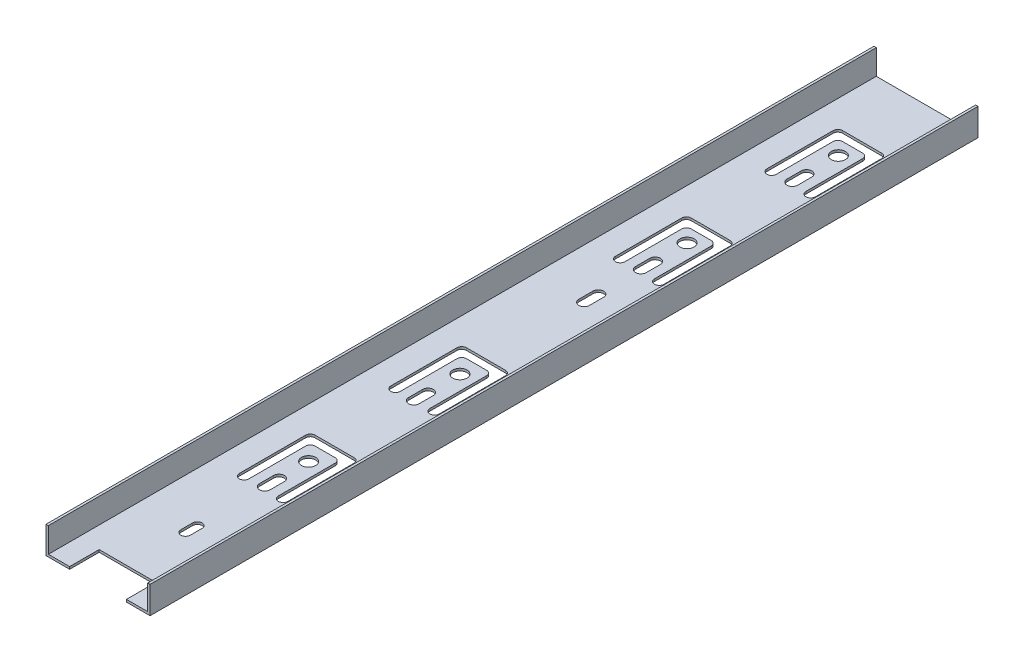
SolidWorks part; units mm, degrees
ref_plane "前视基准面" through (0, 0, 0) normal (0, 0, 1) x (1, 0, 0)
ref_plane "上视基准面" through (0, 0, 0) normal (0, 1, 0) x (1, 0, 0)
ref_plane "右视基准面" through (0, 0, 0) normal (1, 0, 0) x (0, 0, -1)
sketch "草图1" plane through (0, 0, 0) normal (0, 0, 1) x (1, 0, 0)
  line L0 (-12.1861, 22.9643) -> (-12.1861, -29.0019) construction
  line L1 (-34.1861, 5.4117) -> (-33.1861, 5.4117)
  line L2 (-34.1861, 5.4117) -> (-34.1861, -6.0883)
  line L3 (-34.1861, -6.0883) -> (9.8139, -6.0883)
  line L4 (9.8139, 5.4117) -> (9.8139, -6.0883)
  line L6 (-33.1861, 5.4117) -> (-33.1861, -5.0883)
  line L7 (-33.1861, -5.0883) -> (8.8139, -5.0883)
  line L8 (8.8139, 5.4117) -> (8.8139, -5.0883)
  line L9 (8.8139, 5.4117) -> (9.8139, 5.4117)
  dimension "D1" = 11.5
  dimension "D2" = 44
  dimension "D3" = 1
  dimension "D4" = 1
extrude "凸台-拉伸1" add sketch "草图1" along normal blind 350
sketch "草图2" plane through (0, -6.0883, 0) normal (0, -1, 0) x (1, 0, 0)
  line L0 (-12.1861, 366.3647) -> (-12.1861, -33.8087) construction
  line L1 (-34.1861, 350) -> (-34.1861, 0) construction
  line L2 (9.8139, 350) -> (9.8139, 0) construction
  line L3 (-34.1861, 350) -> (9.8139, 350) construction
  line L6 (-22.4361, 280) -> (-22.4361, 252)
  line L7 (-20.4361, 250) -> (-3.9361, 250)
  line L8 (-1.9361, 280) -> (-1.9361, 252)
  line L10 (-18.4361, 280) -> (-18.4361, 256)
  line L11 (-16.4361, 254) -> (-7.9361, 254)
  line L12 (-5.9361, 280) -> (-5.9361, 256)
  line L13 (-14.4361, 279.5) -> (-14.4361, 273.5)
  line L14 (-9.9361, 279.5) -> (-9.9361, 273.5)
  line L15 (-5.9361, 216) -> (-5.9361, 192)
  line L16 (-16.4361, 190) -> (-7.9361, 190)
  line L17 (-14.4361, 216.5) -> (-14.4361, 210.5)
  line L18 (-18.4361, 216) -> (-18.4361, 192)
  line L19 (-22.4361, 216) -> (-22.4361, 188)
  line L20 (-9.9361, 216.5) -> (-9.9361, 210.5)
  line L21 (-1.9361, 216) -> (-1.9361, 188)
  line L22 (-20.4361, 186) -> (-3.9361, 186)
  line L23 (-20.4361, 91) -> (-3.9361, 91)
  line L24 (-9.9361, 120.5) -> (-9.9361, 114.5)
  line L25 (-16.4361, 95) -> (-7.9361, 95)
  line L26 (-5.9361, 121) -> (-5.9361, 97)
  line L27 (-14.4361, 120.5) -> (-14.4361, 114.5)
  line L28 (-18.4361, 121) -> (-18.4361, 97)
  line L29 (-22.4361, 121) -> (-22.4361, 93)
  line L30 (-1.9361, 121) -> (-1.9361, 93)
  line L31 (-20.4361, 27) -> (-3.9361, 27)
  line L32 (-9.9361, 56.5) -> (-9.9361, 50.5)
  line L33 (-16.4361, 31) -> (-7.9361, 31)
  line L34 (-5.9361, 57) -> (-5.9361, 33)
  line L35 (-14.4361, 56.5) -> (-14.4361, 50.5)
  line L36 (-18.4361, 57) -> (-18.4361, 33)
  line L37 (-22.4361, 57) -> (-22.4361, 29)
  line L38 (-1.9361, 57) -> (-1.9361, 29)
  line L39 (-14.1861, 313) -> (-14.1861, 308)
  line L40 (-10.1861, 313) -> (-10.1861, 308)
  line L41 (-14.4361, 144.5) -> (-14.4361, 138.5)
  line L42 (-24.1861, 350) -> (-0.1861, 350)
  line L43 (-24.1861, 350) -> (-24.1861, 337.5344)
  line L44 (-24.1861, 337.5344) -> (-0.1861, 337.5344)
  line L45 (-0.1861, 350) -> (-0.1861, 337.5344)
  line L46 (-9.9361, 144.5) -> (-9.9361, 138.5)
  circle A0 centre (-12.1861, 261) radius 3
  arc A5 (-1.9361, 252) -> (-3.9361, 250) centre (-3.9361, 252) cw
  arc A6 (-20.4361, 250) -> (-22.4361, 252) centre (-20.4361, 252) cw
  arc A7 (-16.4361, 254) -> (-18.4361, 256) centre (-16.4361, 256) cw
  arc A8 (-7.9361, 254) -> (-5.9361, 256) centre (-7.9361, 256) ccw
  arc A10 (-9.9361, 279.5) -> (-14.4361, 279.5) centre (-12.1861, 279.5) ccw
  arc A11 (-14.4361, 273.5) -> (-9.9361, 273.5) centre (-12.1861, 273.5) ccw
  arc A12 (-18.4361, 280) -> (-22.4361, 280) centre (-20.4361, 280) ccw
  arc A13 (-1.9361, 280) -> (-5.9361, 280) centre (-3.9361, 280) ccw
  arc A14 (-1.9361, 216) -> (-5.9361, 216) centre (-3.9361, 216) ccw
  arc A15 (-9.9361, 216.5) -> (-14.4361, 216.5) centre (-12.1861, 216.5) ccw
  arc A16 (-18.4361, 216) -> (-22.4361, 216) centre (-20.4361, 216) ccw
  circle A17 centre (-12.1861, 197) radius 3
  arc A18 (-7.9361, 190) -> (-5.9361, 192) centre (-7.9361, 192) ccw
  arc A19 (-1.9361, 188) -> (-3.9361, 186) centre (-3.9361, 188) cw
  arc A20 (-20.4361, 186) -> (-22.4361, 188) centre (-20.4361, 188) cw
  arc A21 (-14.4361, 210.5) -> (-9.9361, 210.5) centre (-12.1861, 210.5) ccw
  arc A22 (-16.4361, 190) -> (-18.4361, 192) centre (-16.4361, 192) cw
  arc A23 (-20.4361, 91) -> (-22.4361, 93) centre (-20.4361, 93) cw
  arc A24 (-18.4361, 121) -> (-22.4361, 121) centre (-20.4361, 121) ccw
  arc A25 (-14.4361, 114.5) -> (-9.9361, 114.5) centre (-12.1861, 114.5) ccw
  arc A26 (-1.9361, 121) -> (-5.9361, 121) centre (-3.9361, 121) ccw
  arc A27 (-16.4361, 95) -> (-18.4361, 97) centre (-16.4361, 97) cw
  arc A28 (-9.9361, 120.5) -> (-14.4361, 120.5) centre (-12.1861, 120.5) ccw
  arc A29 (-7.9361, 95) -> (-5.9361, 97) centre (-7.9361, 97) ccw
  arc A30 (-1.9361, 93) -> (-3.9361, 91) centre (-3.9361, 93) cw
  circle A31 centre (-12.1861, 101) radius 3
  arc A32 (-20.4361, 27) -> (-22.4361, 29) centre (-20.4361, 29) cw
  arc A33 (-18.4361, 57) -> (-22.4361, 57) centre (-20.4361, 57) ccw
  arc A34 (-14.4361, 50.5) -> (-9.9361, 50.5) centre (-12.1861, 50.5) ccw
  arc A35 (-1.9361, 57) -> (-5.9361, 57) centre (-3.9361, 57) ccw
  arc A36 (-16.4361, 31) -> (-18.4361, 33) centre (-16.4361, 33) cw
  arc A37 (-9.9361, 56.5) -> (-14.4361, 56.5) centre (-12.1861, 56.5) ccw
  arc A38 (-7.9361, 31) -> (-5.9361, 33) centre (-7.9361, 33) ccw
  arc A39 (-1.9361, 29) -> (-3.9361, 27) centre (-3.9361, 29) cw
  circle A40 centre (-12.1861, 37) radius 3
  arc A41 (-10.1861, 313) -> (-14.1861, 313) centre (-12.1861, 313) ccw
  arc A42 (-14.1861, 308) -> (-10.1861, 308) centre (-12.1861, 308) ccw
  arc A43 (-14.4361, 138.5) -> (-9.9361, 138.5) centre (-12.1861, 138.5) ccw
  arc A44 (-9.9361, 144.5) -> (-14.4361, 144.5) centre (-12.1861, 144.5) ccw
  point P26 (-22.4361, 282)
  point P31 (-22.4361, 250)
  dimension "D1" = 6
  dimension "D2" = 89
  dimension "D3" = 64
  dimension "D4" = 96
  dimension "D5" = 64
  dimension "D6" = 11
  dimension "D11" = 4
  dimension "D12" = 2
  dimension "D13" = 4.5
  dimension "D9" = 2
  dimension "D16" = 11
  dimension "D17" = 5
  dimension "D18" = 4
  dimension "D7" = 20.5
  dimension "D8" = 32
  dimension "D10" = 4
  dimension "D14" = 6
  dimension "D15" = 12.5
  dimension "D19" = 52
  dimension "D20" = 24
  dimension "D21" = 24
extrude "切除-拉伸1" cut sketch "草图2" against normal blind 350
